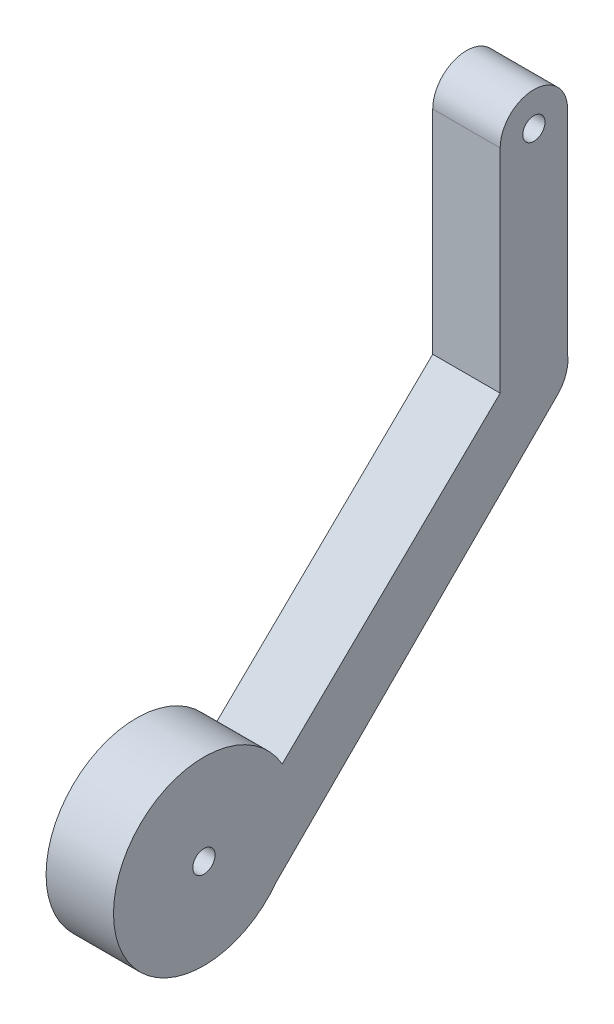
SolidWorks part; units mm, degrees
ref_plane "前视基准面" through (0, 0, 0) normal (0, 0, 1) x (1, 0, 0)
ref_plane "上视基准面" through (0, 0, 0) normal (0, 1, 0) x (1, 0, 0)
ref_plane "右视基准面" through (0, 0, 0) normal (1, 0, 0) x (0, 0, -1)
sketch "草图1" plane through (56.4159, 0, 0) normal (1, 0, 0) x (0, 0, -1)
  line L1 (-55.2644, -53.1536) -> (-87.5837, -84.6062)
  line L3 (-45.2644, -21.6631) -> (-45.2644, -53.1536)
  line L5 (-55.2644, -21.6631) -> (-55.2644, -53.1536)
  line L7 (-88.4125, -99.2767) -> (-46.78, -57.6442)
  arc A0 (-45.2644, -21.6631) -> (-55.2644, -21.6631) centre (-50.2644, -21.6631) ccw
  arc A2 (-46.78, -57.6442) -> (-45.2644, -53.1536) centre (-50.5553, -53.8689) ccw
  arc A3 (-88.4125, -99.2767) -> (-87.5837, -84.6062) centre (-99.1903, -91.3091) cw
  circle A4 centre (-50.2644, -21.6631) radius 1.65
  circle A5 centre (-99.1903, -91.3091) radius 1.65
  point P11 (0, 0)
  dimension "D1" = 3.3
  dimension "D2" = 3.3
extrude "凸台-拉伸1" add sketch "草图1" along normal blind 10
